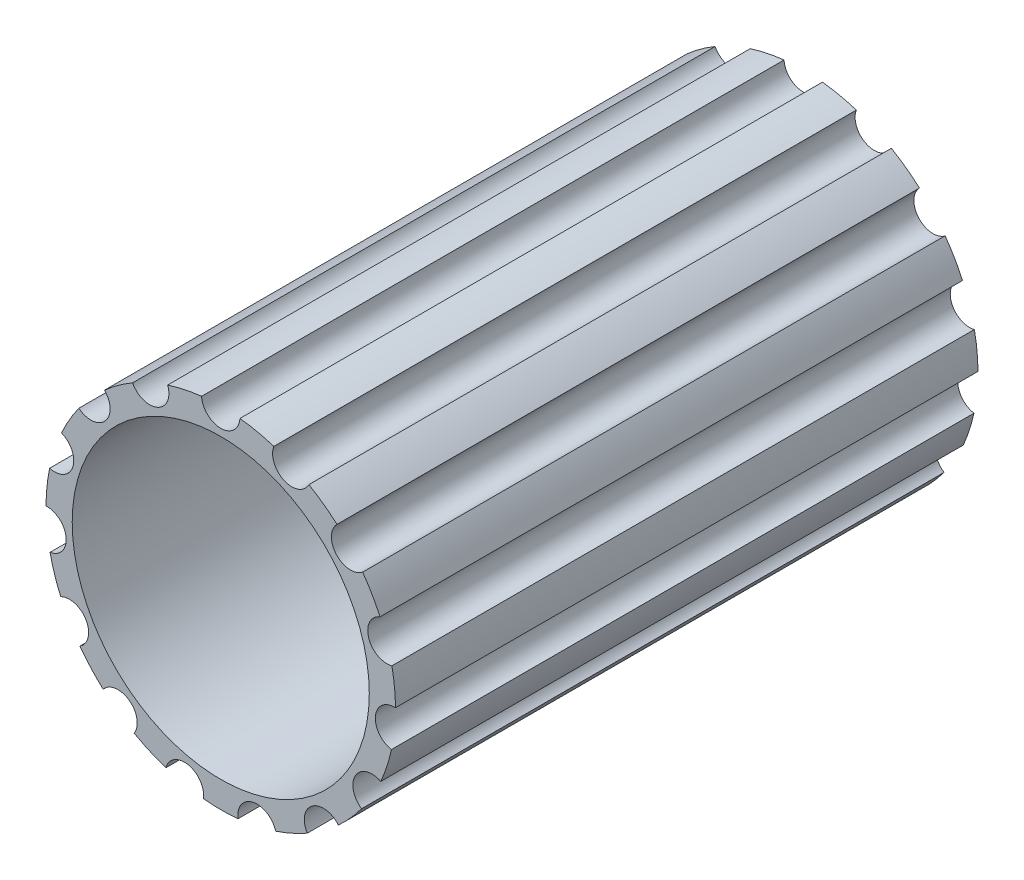
SolidWorks part; units mm, degrees
ref_plane "Front Plane" through (0, 0, 0) normal (0, 0, 1) x (1, 0, 0)
ref_plane "Top Plane" through (0, 0, 0) normal (0, 1, 0) x (1, 0, 0)
ref_plane "Right Plane" through (0, 0, 0) normal (1, 0, 0) x (0, 0, -1)
sketch "Sketch1" plane through (0, 0, 0) normal (0, 0, 1) x (1, 0, 0)
  arc A0 (0.3294, 2.9819) -> (0.9119, 2.858) centre (0, 0) cw
  arc A1 (-0.3294, 2.9819) -> (0.3294, 2.9819) centre (0, 3) ccw
  arc A2 (1.5137, 2.5901) -> (1.9956, 2.24) centre (0, 0) cw
  arc A3 (0.9119, 2.858) -> (1.5137, 2.5901) centre (1.2202, 2.7406) ccw
  arc A4 (2.4364, 1.7505) -> (2.7341, 1.2347) centre (0, 0) cw
  arc A5 (1.9956, 2.24) -> (2.4364, 1.7505) centre (2.2294, 2.0074) ccw
  arc A6 (2.9377, 0.6082) -> (3, 0.0159) centre (0, 0) cw
  arc A7 (2.7341, 1.2347) -> (2.9377, 0.6082) centre (2.8532, 0.9271) ccw
  arc A8 (2.9311, -0.6393) -> (2.7471, -1.2057) centre (0, 0) cw
  arc A9 (3, 0.0159) -> (2.9311, -0.6393) centre (2.9836, -0.3136) ccw
  arc A10 (2.4177, -1.7762) -> (2.0192, -2.2188) centre (0, 0) cw
  arc A11 (2.7471, -1.2057) -> (2.4177, -1.7762) centre (2.5981, -1.5) ccw
  arc A12 (1.4862, -2.606) -> (0.9422, -2.8482) centre (0, 0) cw
  arc A13 (2.0192, -2.2188) -> (1.4862, -2.606) centre (1.7634, -2.4271) ccw
  arc A14 (0.2978, -2.9852) -> (-0.2978, -2.9852) centre (0, 0) cw
  arc A15 (0.9422, -2.8482) -> (0.2978, -2.9852) centre (0.6237, -2.9344) ccw
  arc A16 (-0.9422, -2.8482) -> (-1.4862, -2.606) centre (0, 0) cw
  arc A17 (-0.2978, -2.9852) -> (-0.9422, -2.8482) centre (-0.6237, -2.9344) ccw
  arc A18 (-2.0192, -2.2188) -> (-2.4177, -1.7762) centre (0, 0) cw
  arc A19 (-1.4862, -2.606) -> (-2.0192, -2.2188) centre (-1.7634, -2.4271) ccw
  arc A20 (-2.7471, -1.2057) -> (-2.9311, -0.6393) centre (0, 0) cw
  arc A21 (-2.4177, -1.7762) -> (-2.7471, -1.2057) centre (-2.5981, -1.5) ccw
  arc A22 (-3, 0.0159) -> (-2.9377, 0.6082) centre (0, 0) cw
  arc A23 (-2.9311, -0.6393) -> (-3, 0.0159) centre (-2.9836, -0.3136) ccw
  arc A24 (-2.7341, 1.2347) -> (-2.4364, 1.7505) centre (0, 0) cw
  arc A25 (-2.9377, 0.6082) -> (-2.7341, 1.2347) centre (-2.8532, 0.9271) ccw
  arc A26 (-1.9956, 2.24) -> (-1.5137, 2.5901) centre (0, 0) cw
  arc A27 (-2.4364, 1.7505) -> (-1.9956, 2.24) centre (-2.2294, 2.0074) ccw
  arc A28 (-0.9119, 2.858) -> (-0.3294, 2.9819) centre (0, 0) cw
  arc A29 (-1.5137, 2.5901) -> (-0.9119, 2.858) centre (-1.2202, 2.7406) ccw
  point P64 (0, 0)
  dimension "D2" = 15
extrude "Boss-Extrude1" add sketch "Sketch1" along normal blind 10
sketch "Sketch2" plane through (0, 0, 10) normal (0, 0, 1) x (1, 0, 0)
  circle A0 centre (0, 0) radius 2.55
extrude "Cut-Extrude1" cut sketch "Sketch2" against normal blind 10
